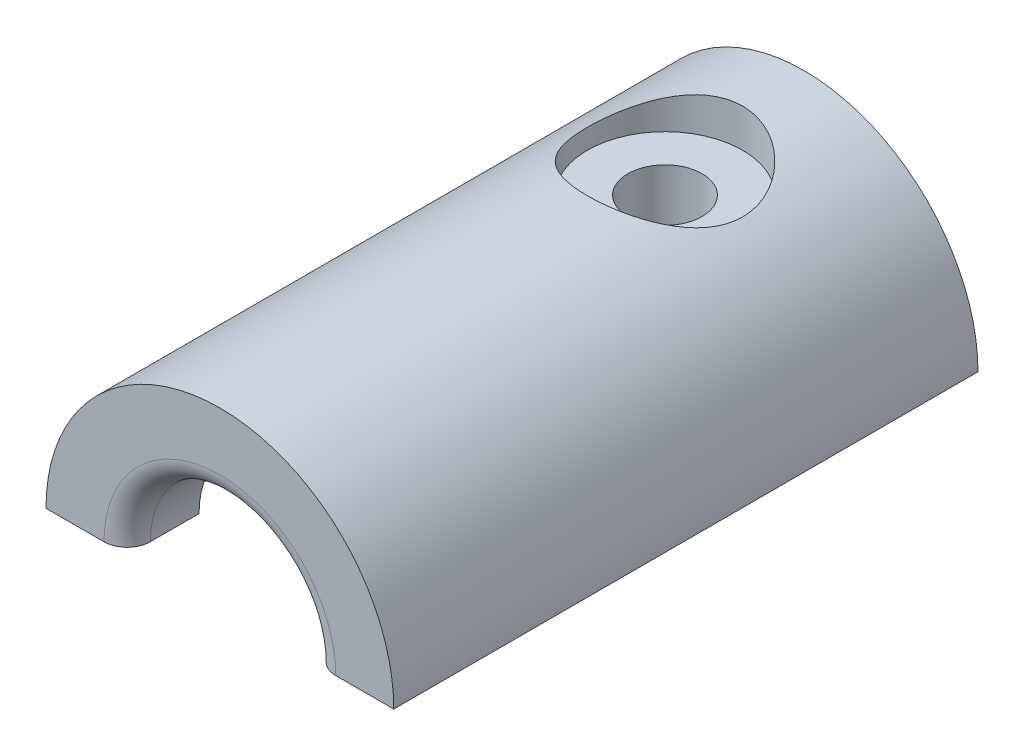
SolidWorks part; units mm, degrees
material "Nylon 101"
ref_plane "Front Plane" through (0, 0, 0) normal (0, 0, 1) x (1, 0, 0)
ref_plane "Top Plane" through (0, 0, 0) normal (0, 1, 0) x (1, 0, 0)
ref_plane "Right Plane" through (0, 0, 0) normal (1, 0, 0) x (0, 0, -1)
sketch "Sketch1" plane through (0, 0, 0) normal (0, 0, 1) x (1, 0, 0)
  circle A0 centre (0, 0) radius 3
  circle A1 centre (0, 0) radius 7.5
  dimension "D1" = 6
  dimension "D2" = 15
extrude "Boss-Extrude1" add sketch "Sketch1" along normal mid plane 15 contours A1 A0
sketch "Sketch2" plane through (0, 0, 7.5) normal (0, 0, 1) x (1, 0, 0)
  circle A0 centre (0, 0) radius 3
  circle A1 centre (0, 0) radius 7.5
  circle A2 centre (0, 0) radius 7.5 construction
  dimension "D1" = 6
extrude "Boss-Extrude2" add sketch "Sketch2" against normal blind 1
sketch "Sketch3" plane through (0, 0, 7.5) normal (0, 0, 1) x (1, 0, 0)
  circle A0 centre (0, 0) radius 4
  circle A1 centre (0, 0) radius 7.5
  circle A2 centre (0, 0) radius 7.5 construction
  dimension "D1" = 8
extrude "Boss-Extrude3" add sketch "Sketch3" along normal blind 3
sketch "Sketch4" plane through (0, 0, 10.5) normal (0, 0, 1) x (1, 0, 0)
  circle A0 centre (0, 0) radius 5.075
  circle A1 centre (0, 0) radius 7.5
  circle A2 centre (0, 0) radius 7.5 construction
  dimension "D1" = 10.15
extrude "Boss-Extrude4" add sketch "Sketch4" along normal blind 4.1
sketch "Sketch5" plane through (0, 0, 14.6) normal (0, 0, 1) x (1, 0, 0)
  circle A0 centre (0, 0) radius 4
  circle A1 centre (0, 0) radius 4 construction
  circle A2 centre (0, 0) radius 7.5
  circle A3 centre (0, 0) radius 7.5 construction
extrude "Boss-Extrude5" add sketch "Sketch5" along normal blind 3.1
ref_plane "Plane1" through (0, 7.5, 0) normal (0, 1, 0) x (1, 0, 0)
sketch "Sketch6" plane through (0, 7.5, 0) normal (0, 1, 0) x (1, 0, 0)
  line L0 (0, -4.125) -> (0, 4.125) construction
  line L2 (7.5, 7.5) -> (-7.5, 7.5) construction
  circle A0 centre (0, 1.5) radius 2.3879
  dimension "D1" = 6
hole_wizard "CBORE for M3 SBHCS1" positions "Sketch7" profile "Sketch8" counterbore size "M3" standard "ANSI Metric"
sketch "Sketch7" plane through (0, 7.5, 0) normal (0, 1, 0) x (1, 0, 0)
  line L0 (0, -4.125) -> (0, 4.125) construction
  line L1 (7.5, 7.5) -> (-7.5, 7.5) construction
  point P0 (0, 1.5)
  dimension "D1" = 6
sketch "Sketch8" plane through (0, 7.5, -1.5) normal (1, 0, 0) x (0, 0, 1)
  line L0 (0, 0) -> (0, 10.9614)
  line L1 (0, 10.9614) -> (1.6, 10)
  line L2 (1.6, 10) -> (1.6, 1.65)
  line L3 (1.6, 1.65) -> (3.35, 1.65)
  line L4 (3.35, 1.65) -> (3.35, 0)
  line L5 (3.35, 0) -> (0, 0)
  line L10 (0, 10.9614) -> (-1.6, 10) construction
  line L11 (0, -6.35) -> (0, 107.95) construction
  dimension "Hole Dia." = 3.2
  dimension "Hole Depth" = 10
  dimension "C'Bore Dia." = 6.7
  dimension "C'Bore Depth" = 1.65
  dimension "Drill Angle" = 118
sketch "Sketch9" plane through (0, 0, 0) normal (0, 1, 0) x (1, 0, 0)
  line L1 (-7.5, 7.5) -> (7.5, 7.5)
  line L2 (-7.5, 7.5) -> (-7.5, -17.7)
  line L3 (-7.5, -17.7) -> (7.5, -17.7)
  line L4 (7.5, 7.5) -> (7.5, -17.7)
extrude "Cut-Extrude2" cut sketch "Sketch9" against normal through all
fillet "Fillet1" radius 1 1 edges at (0, 4, 17.7)
fillet "Fillet2" radius 2 1 edges at (0, 3, -7.5)
